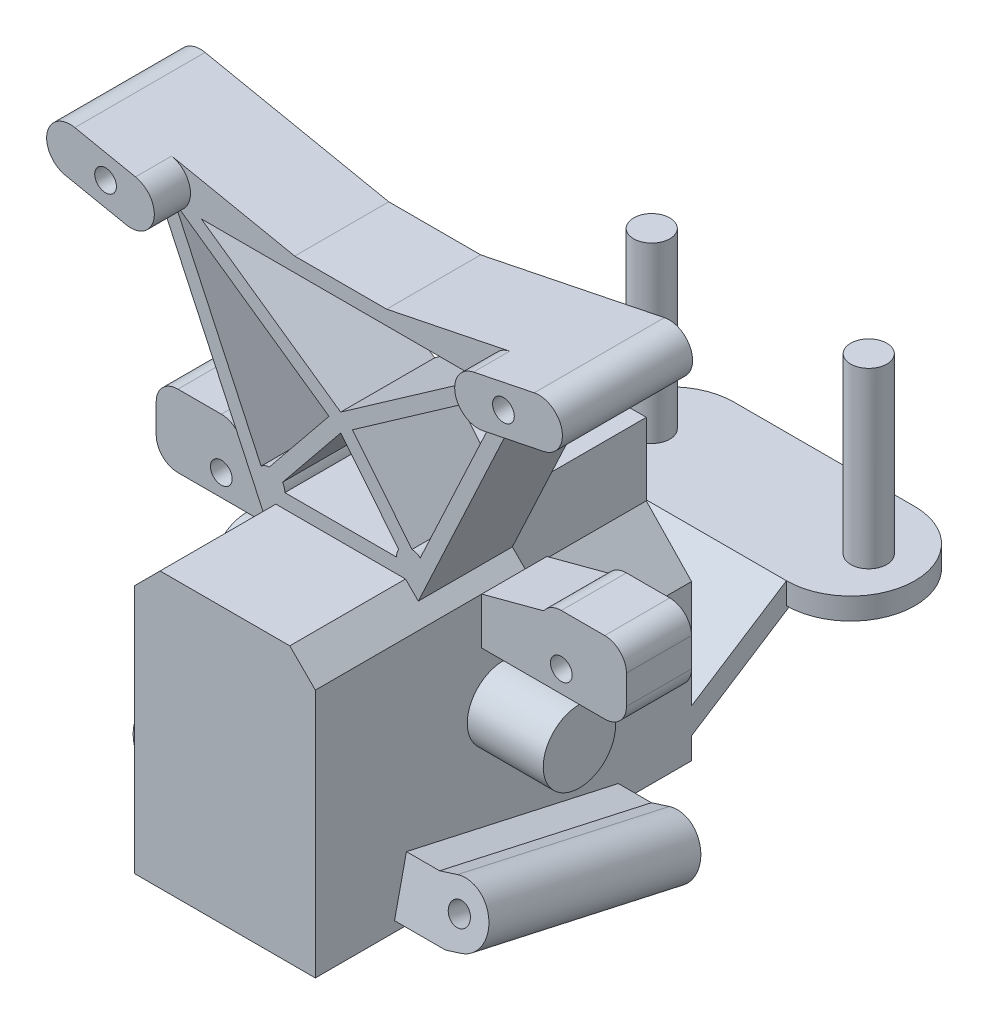
SolidWorks part; units mm, degrees
ref_plane "Front Plane" through (0, 0, 0) normal (0, 0, 1) x (1, 0, 0)
ref_plane "Top Plane" through (0, 0, 0) normal (0, 1, 0) x (1, 0, 0)
ref_plane "Right Plane" through (0, 0, 0) normal (1, 0, 0) x (0, 0, -1)
sketch "Sketch1" plane through (0, 0, 0) normal (1, 0, 0) x (0, 0, -1)
  circle A0 centre (0, 0) radius 5
  dimension "D1" = 10
extrude "Driveline Axis" add sketch "Sketch1" along normal mid plane 46 contours A0
sketch "Sketch2" plane through (0, 0, 0) normal (0, 0, 1) x (1, 0, 0)
  line L0 (-12.5, -20) -> (-12.5, 14.4645)
  line L1 (-12.5, 14.4645) -> (-8.9645, 18)
  line L2 (-8.9645, 18) -> (8.9645, 18)
  line L3 (8.9645, 18) -> (12.5, 14.4645)
  line L4 (12.5, 14.4645) -> (12.5, -20)
  line L5 (12.5, -20) -> (-12.5, -20)
  dimension "D1" = 20
  dimension "D2" = 18
  dimension "D3" = 5
  dimension "D4" = 5
  dimension "D5" = 25
  dimension "D6" = 12.5
extrude "Dummy Boss" add sketch "Sketch2" along normal mid plane 52
ref_plane "Pin Base Plane" through (0, 0, -18) normal (0, 0, -1) x (-1, 0, 0)
sketch "Sketch8" plane through (0, 0, 0) normal (0, 0, 1) x (1, 0, 0)
  line L0 (-10.7322, 16.2322) -> (-24.6615, 46.1036)
  line L1 (-8.9645, 18) -> (-12.5, 14.4645) construction
  line L2 (-24.6615, 46.1036) -> (-33.049, 47.8157)
  line L3 (-31.749, 54.1843) -> (-6.351, 49)
  line L4 (9.8662, 21.9942) -> (1.6121, 32.1873)
  line L5 (-6.351, 49) -> (6.351, 49)
  line L6 (0, 49) -> (0, 18) construction
  line L7 (8.9645, 18) -> (-8.9645, 18) construction
  line L8 (8.9645, 18) -> (-8.9645, 18)
  line L9 (-8.9645, 18) -> (-10.7322, 16.2322)
  line L10 (7.7145, 20) -> (-7.7145, 20)
  line L11 (-10.9977, 21.534) -> (-22.924, 47.11)
  line L12 (-8.032, 21.0813) -> (0, 31)
  line L13 (-9.8662, 21.9942) -> (-1.6121, 32.1873)
  line L14 (-1.6121, 32.1873) -> (-22.924, 47.11)
  line L15 (-19.28, 47) -> (0, 33.5)
  line L16 (8.032, 21.0813) -> (0, 31)
  line L17 (-19.28, 47) -> (19.28, 47)
  line L18 (8.9645, 18) -> (10.7322, 16.2322)
  line L19 (19.28, 47) -> (0, 33.5)
  line L20 (1.6121, 32.1873) -> (22.924, 47.11)
  line L21 (10.9977, 21.534) -> (22.924, 47.11)
  line L22 (10.7322, 16.2322) -> (24.6615, 46.1036)
  line L23 (24.6615, 46.1036) -> (33.049, 47.8157)
  line L24 (31.749, 54.1843) -> (6.351, 49)
  arc A0 (-33.049, 47.8157) -> (-31.749, 54.1843) centre (-32.399, 51) cw
  arc A1 (-7.7145, 20) -> (-8.032, 21.0813) centre (-9.7145, 20) ccw
  arc A2 (-9.8662, 21.9942) -> (-10.9977, 21.534) centre (-9.7145, 20) ccw
  circle A4 centre (-27.5, 50) radius 1.5
  arc A6 (9.8662, 21.9942) -> (10.9977, 21.534) centre (9.7145, 20) cw
  arc A7 (7.7145, 20) -> (8.032, 21.0813) centre (9.7145, 20) cw
  arc A8 (33.049, 47.8157) -> (31.749, 54.1843) centre (32.399, 51) ccw
  circle A10 centre (27.5, 50) radius 1.5
  point P32 (-5.7392, 27.0907)
  point P50 (0, 20)
  point P52 (0, 47)
  dimension "D1" = 2
  dimension "D6" = 2
  dimension "D10" = 3.25
  dimension "D11" = 55
  dimension "D12" = 29
  dimension "D13" = 3
  dimension "D2" = 2
  dimension "D3" = 2
  dimension "D4" = 2
  dimension "D5" = 2
  dimension "D7" = 0.75
  dimension "D8" = 2
  dimension "D9" = 50
  dimension "D14" = 5
  dimension "D15" = 86
  dimension "D16" = 3.25
  dimension "D17" = 64
  dimension "D18" = 11
  dimension "D19" = 51
  dimension "D20" = 33
  dimension "D24" = 2.5
extrude "Uprights" add sketch "Sketch8" along normal blind 10 and the other way blind 3 contours A2 L13 L14 L11 | L17 L6 L19 | L6 L17 L15 | L4 A6 L21 L20 | L16 L6 L10 A7 | L6 L12 A1 L10 | A4 | A10 | L22 L23 A8 L24 L5 L3 A0 L2 L0 L9 L8 L18
sketch "Sketch9" plane through (0, 0, 10) normal (0, 0, 1) x (1, 0, 0)
  line L0 (-24.6615, 46.1036) -> (-33.049, 47.8157)
  line L1 (-31.749, 54.1843) -> (-23.3615, 52.4722)
  line L2 (-31.749, 54.1843) -> (-6.351, 49) construction
  line L3 (23.3615, 52.4722) -> (31.749, 54.1843)
  line L4 (31.749, 54.1843) -> (6.351, 49) construction
  line L5 (33.049, 47.8157) -> (24.6615, 46.1036)
  circle A0 centre (-27.5, 50) radius 1.5
  circle A1 centre (27.5, 50) radius 1.5
  circle A2 centre (27.5, 50) radius 1.5 construction
  circle A3 centre (-27.5, 50) radius 1.5 construction
  arc A4 (-33.049, 47.8157) -> (-31.749, 54.1843) centre (-32.399, 51) cw
  arc A5 (-31.749, 54.1843) -> (-33.049, 47.8157) centre (-32.399, 51) ccw construction
  arc A6 (-23.3615, 52.4722) -> (-24.6615, 46.1036) centre (-24.0115, 49.2879) cw
  arc A7 (31.749, 54.1843) -> (33.049, 47.8157) centre (32.399, 51) cw
  arc A8 (24.6615, 46.1036) -> (23.3615, 52.4722) centre (24.0115, 49.2879) cw
extrude "Shock Mount" add sketch "Sketch9" along normal blind 5 and the other way blind 13
sketch "Sketch10" plane through (0, 0, 0) normal (0, 0, 1) x (1, 0, 0)
  line L0 (29.5, 8) -> (12.5, 8)
  line L1 (-12.5, 14.4645) -> (-21.0556, 16.7392)
  line L2 (32.5, 11) -> (32.5, 15)
  line L3 (29.5, 18) -> (23.5, 18)
  line L4 (0, 41.2363) -> (0, 7.9844) construction
  line L5 (12.5, 8) -> (12.5, 14.4645)
  line L6 (12.5, 14.4645) -> (21.0556, 16.7392)
  line L7 (-12.5, 8) -> (-12.5, 14.4645)
  line L8 (-29.5, 18) -> (-23.5, 18)
  line L9 (-32.5, 11) -> (-32.5, 15)
  line L10 (-29.5, 8) -> (-12.5, 8)
  line L11 (12.5, -20) -> (12.5, 14.4645) construction
  arc A0 (29.5, 8) -> (32.5, 11) centre (29.5, 11) ccw
  circle A1 centre (23.5, 11) radius 1.5
  arc A2 (21.0556, 16.7392) -> (23.5, 18) centre (23.5, 15) cw
  arc A3 (29.5, 18) -> (32.5, 15) centre (29.5, 15) cw
  arc A4 (-29.5, 18) -> (-32.5, 15) centre (-29.5, 15) ccw
  arc A5 (-21.0556, 16.7392) -> (-23.5, 18) centre (-23.5, 15) ccw
  circle A6 centre (-23.5, 11) radius 1.5
  arc A7 (-29.5, 8) -> (-32.5, 11) centre (-29.5, 11) cw
  dimension "D1" = 3
  dimension "D2" = 3
  dimension "D3" = 3
  dimension "D4" = 4
  dimension "D6" = 3
  dimension "D5" = 6
  dimension "D7" = 47
  dimension "D10" = 11
extrude "Turnbuckle Mounts" add sketch "Sketch10" against normal blind 6 and the other way blind 3
sketch "Sketch11" plane through (0, 0, -26) normal (0, 0, -1) x (-1, 0, 0)
  line L0 (-12.5, 1.4645) -> (-6.25, 8)
  line L1 (-12.5, -20) -> (-12.5, 14.4645) construction
  line L2 (-6.25, 8) -> (-6.25, 18)
  line L3 (-8.9645, 18) -> (8.9645, 18) construction
  line L4 (5.75, 18) -> (8.9645, 18)
  line L5 (-8.9645, 18) -> (8.9645, 18) construction
  line L6 (5.75, 18) -> (5.75, 8)
  line L7 (5.75, 8) -> (12.5, 1.5449)
  line L8 (12.5, 14.4645) -> (12.5, -20) construction
  line L9 (-12.5, 1.4645) -> (-12.5, 14.4645)
  line L10 (-6.25, 18) -> (-8.9645, 18)
  line L11 (8.9645, 18) -> (12.5, 14.4645)
  line L13 (8.9645, 18) -> (10.7322, 16.2322) construction
  line L14 (12.5, 14.4645) -> (12.5, 1.5449)
  line L15 (12.5, 1.5449) -> (12.5075, 1.5371)
  line L16 (-8.9645, 18) -> (-12.5, 14.4645)
  line L17 (-12.5, 14.4645) -> (-12.5234, 14.4847)
  line L18 (-12.5, 14.4645) -> (-8.9645, 18) construction
  line M5 (12.5, -20) -> (12.5, 14.4645)
  line M6 (12.5, 14.4645) -> (8.9645, 18)
  line M7 (8.9645, 18) -> (-8.9645, 18)
  line M8 (-8.9645, 18) -> (-12.5, 14.4645)
  line M9 (-12.5, 14.4645) -> (-12.5, -20)
  dimension "D1" = 12
  dimension "D2" = 10
  dimension "D3" = 6.25
extrude "Turnbuckle Room" cut sketch "Sketch11" against normal blind 23 and the other way through all contours L6 L7 M5 M6 M7 | L0 L2 M7 M8 M9
sketch "Sketch40" plane through (0, 0, 0) normal (1, 0, 0) x (0, 0, -1)
  line L0 (26, -13.4336) -> (39.1189, -5)
  line L1 (26, -20) -> (26, 1.4645) construction
  line L2 (26, -17) -> (40, -8)
  line L5 (39.1189, -5) -> (56.8811, -5)
  line L6 (56.8811, -5) -> (56.8811, -8)
  line L7 (56.8811, -8) -> (40, -8)
  line L8 (26, -13.4336) -> (26, -17)
  line L9 (48, -5) -> (48, -8) construction
  line L10 (26, -20) -> (58.296, -20) construction
  line L11 (-26, 4.7618) -> (-26, -8.0225) construction
  line L12 (-26, -20) -> (-26, 14.4645) construction
  point P15 (32.5594, -9.2168)
  dimension "D1" = 3
  dimension "D2" = 3
  dimension "D3" = 74
  dimension "D4" = 0
  dimension "D5" = 15
  dimension "D6" = 3
  dimension "D7" = 14
extrude "Boss-Extrude2" add sketch "Sketch40" along normal mid plane 25
sketch "Sketch41" plane through (0, -5, 0) normal (0, 1, 0) x (1, 0, 0)
  line L0 (12.5, 56.8811) -> (12.5, 39.1189) construction
  line L1 (12.5, 56.8811) -> (12.5, 39.1189)
  arc A0 (12.5, 39.1189) -> (12.5, 56.8811) centre (12.5, 48) ccw
extrude "Boss-Extrude3" add sketch "Sketch41" against normal up to surface (3 mm away) up to face at (0, -8, -48.4406)
mirror "Mirror4" about plane through (0, 0, 0) normal (1, 0, 0) of "Boss-Extrude3"
sketch "Sketch43" plane through (0, -5, 0) normal (0, 1, 0) x (1, 0, 0)
  line L0 (-21.3811, 48) -> (21.3811, 48) construction
  line L1 (0, 61.4593) -> (0, 50.7815) construction
  arc A0 (-12.5, 56.8811) -> (-12.5, 39.1189) centre (-12.5, 48) ccw construction
  arc A1 (12.5, 39.1189) -> (12.5, 56.8811) centre (12.5, 48) ccw construction
  circle A2 centre (-15, 48) radius 2.5
  circle A3 centre (15, 48) radius 2.5
  dimension "D1" = 5
  dimension "D2" = 5
  dimension "D3" = 30
  dimension "D4" = 15
extrude "Boss-Extrude4" add sketch "Sketch43" along normal blind 24
sketch "Sketch46" plane through (12.5, 0, 0) normal (1, 0, 0) x (0, 0, -1)
  line L0 (0, -20) -> (8.0677, 16.3909) construction
  line L1 (0, 39.2139) -> (0, -39.2139) construction
  line L3 (-26, -20) -> (26, -20) construction
  dimension "D1" = 12.5
ref_plane "Plane1" through (0, -0.9369, -4.2262) normal (0, -0.2164, -0.9763) x (0, 0.9763, -0.2164)
sketch "Sketch47" plane through (0, -0.9369, -4.2262) normal (0, -0.2164, -0.9763) x (0, 0.9763, -0.2164)
  line L0 (-13.8066, 12.5) -> (-13.8066, 17.084)
  line L1 (-19.5259, 12.5) -> (17.7485, 12.5) construction
  line L2 (-13.8066, 17.084) -> (-13.1499, 19.4154)
  line L3 (-20.8501, 21.5846) -> (-21.4233, 19.5501)
  line L5 (-21.4233, 19.5501) -> (-21.4233, 12.5)
  line L6 (-21.4233, 12.5) -> (-13.8066, 12.5)
  arc A0 (-13.1499, 19.4154) -> (-20.8501, 21.5846) centre (-17, 20.5) ccw
  dimension "D1" = 4
  dimension "D2" = 17
  dimension "D3" = 20.5
extrude "Boss-Extrude5" add sketch "Sketch47" along normal mid plane 30
sketch "Sketch48" plane through (12.5, 0, 0) normal (-1, 0, 0) x (0, 0, 1)
  line L0 (-14.2338, -25.099) -> (8.7663, -20)
  line L1 (8.7663, -20) -> (-15.3642, -20)
  line L2 (-15.3642, -20) -> (-14.2338, -25.099)
extrude "Boss-Extrude6" add sketch "Sketch48" along normal up to surface (12.5 mm away) up to plane "Right Plane"
sketch "Sketch49" plane through (0, -0.9369, -4.2262) normal (0, -0.2164, -0.9763) x (0, 0.9763, -0.2164)
  circle A0 centre (-17, 20.5) radius 1.5
  arc A1 (-13.1499, 19.4154) -> (-20.8501, 21.5846) centre (-17, 20.5) ccw construction
  dimension "D1" = 3
extrude "Cut-Extrude1" cut sketch "Sketch49" against normal mid plane 30
mirror "Mirror5" about plane through (0, 0, 0) normal (1, 0, 0) of "Cut-Extrude1", "Boss-Extrude6", "Boss-Extrude5"
